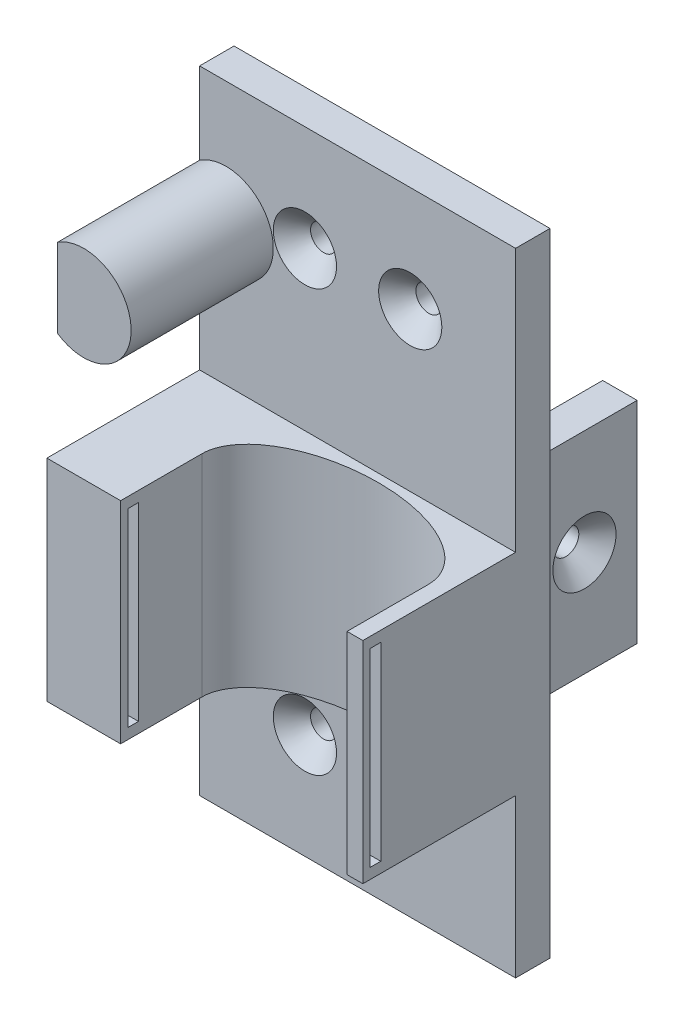
SolidWorks part; units mm, degrees
ref_plane "Front Plane" through (0, 0, 0) normal (0, 0, 1) x (1, 0, 0)
ref_plane "Top Plane" through (0, 0, 0) normal (0, 1, 0) x (1, 0, 0)
ref_plane "Right Plane" through (0, 0, 0) normal (1, 0, 0) x (0, 0, -1)
sketch "Sketch1" plane through (0, 0, 0) normal (0, 0, 1) x (1, 0, 0)
  line L1 (-30, 60) -> (30, 60)
  line L2 (-30, 60) -> (-30, -60)
  line L3 (-30, -60) -> (30, -60)
  line L4 (30, 60) -> (30, -60)
  line L5 (-30, 60) -> (30, -60) construction
  line L6 (-30, -60) -> (30, 60) construction
  point P0 (0, 0)
  dimension "D1" = 60
  dimension "D2" = 120
extrude "Boss-Extrude1" add sketch "Sketch1" along normal blind 6.54
sketch "Sketch7" plane through (0, 0, 6.54) normal (0, 0, 1) x (1, 0, 0)
  line L0 (-30, 60) -> (-30, -60) construction
  line L1 (30, 60) -> (-30, 60) construction
  line L2 (30, -60) -> (30, 60) construction
  line L7 (30, -60) -> (30, 60)
  line L8 (30, 60) -> (-30, 60)
  line L9 (-30, 60) -> (-30, -60)
  line L10 (-30, -60) -> (30, -60)
  line L13 (-30, 44.4833) -> (-30, 29.5167)
  arc A0 (-30, 29.5167) -> (-30, 44.4833) centre (-25, 37) ccw
  dimension "D1" = 9
  dimension "D2" = 23
  dimension "D3" = 55
  dimension "D4" = 0
extrude "Boss-Extrude4" add sketch "Sketch7" along normal blind 27 contours A0 L13
hole_wizard "CSK for M3 Flat Head Machine Screw2" positions "3DSketch1" profile "Sketch9" countersink size "M3" standard "ANSI Metric" end condition through all
sketch3d "3DSketch1"
  line L0 (30, 60, 6.54) -> (-30, 60, 6.54) construction
  line L4 (-30, -60, 6.54) -> (30, -60, 6.54) construction
  line L5 (0, 0, 0) -> (0, 19.3047, 0)
  line L7 (30, -60, 6.54) -> (30, 60, 6.54) construction
  line L8 (-30, 44.4833, 33.54) -> (-30, 29.5167, 33.54) construction
  line L9 (-30, 29.5167, 6.54) -> (-30, -60, 6.54) construction
  point P0 (-10, -40, 6.54)
  point P2 (10, -40, 6.54)
  point P4 (-10, 40, 6.54)
  point P6 (10, 40, 6.54)
  dimension "D1" = 20
  dimension "D2" = 20
  dimension "D3" = 20
  dimension "D6" = 33.6006
  dimension "D4" = 20
  dimension "D5" = 20
  dimension "D9" = 20
  dimension "D7" = 20
  dimension "D8" = 20
sketch "Sketch9" plane through (-10, -40, 6.54) normal (1, 0, 0) x (0, -1, 0)
  line L0 (0, 0) -> (0, 6.54)
  line L1 (0, 6.54) -> (2.465, 6.54)
  line L2 (2.465, 6.54) -> (2.465, 3.535)
  line L3 (2.465, 3.535) -> (6, 0)
  line L5 (6, 0) -> (0, 0)
  line L6 (-2.465, 3.535) -> (-6, 0) construction
  line L11 (0, -6.35) -> (0, 107.95) construction
  dimension "Thru Hole Dia." = 4.93
  dimension "Thru Hole Depth" = 6.54
  dimension "Near C'Sink Dia." = 12
  dimension "Near C'Sink Angle" = 90
sketch "Sketch10" plane through (0, 0, 0) normal (0, 0, -1) x (-1, 0, 0)
  line L1 (20, 20) -> (26.54, 20)
  line L2 (-20, -20) -> (-20, 20)
  line L4 (-20, 20) -> (-26.54, 20)
  line L7 (20, -20) -> (20, 20)
  line L10 (-26.54, 20) -> (-26.54, -20)
  line L11 (-26.54, -20) -> (-20, -20)
  line L12 (26.54, 20) -> (26.54, -20)
  line L13 (26.54, -20) -> (20, -20)
  dimension "D1" = 6.54
  dimension "D2" = 20
  dimension "D3" = 6.54
  dimension "D4" = 20
extrude "Boss-Extrude5" add sketch "Sketch10" along normal blind 20
sketch "Sketch17" plane through (0, 0, 6.54) normal (0, 0, 1) x (1, 0, 0)
  line L0 (-30, 29.5167) -> (-30, -60) construction
  line L1 (-30, 10) -> (30, 10)
  line L2 (-30, 10) -> (-30, -30)
  line L3 (-30, -30) -> (30, -30)
  line L4 (30, 10) -> (30, -30)
  line L5 (30, -60) -> (30, 60) construction
  line L6 (-30, -60) -> (30, -60) construction
  line L7 (30, 60) -> (-30, 60) construction
  dimension "D1" = 40
  dimension "D2" = 30
  dimension "D3" = 50
extrude "Boss-Extrude6" add sketch "Sketch17" along normal blind 29
sketch "Sketch18" plane through (0, 10, 0) normal (0, 1, 0) x (1, 0, 0)
  line L1 (30, -35.54) -> (30, -6.54) construction
  line L2 (30, -35.54) -> (-30, -35.54) construction
  ellipse E0 centre (5.5, -20.092) end of major axis (27, -20.092) minor radius 12
  dimension "D1" = 46
  dimension "D2" = 3
  dimension "D3" = 3.448
extrude "Cut-Extrude1" cut sketch "Sketch18" against normal up to next contours E0
sketch "Sketch21" plane through (0, 0, 35.54) normal (0, 0, 1) x (1, 0, 0)
  line L0 (30, 10) -> (-30, 10) construction
  line L1 (-16, 10) -> (27, 10)
  line L2 (-16, 10) -> (-16, -30)
  line L3 (-16, -30) -> (27, -30)
  line L4 (27, 10) -> (27, -30)
  line L5 (-30, -30) -> (30, -30) construction
  line L6 (30, -30) -> (30, 10) construction
  dimension "D1" = 3
  dimension "D2" = 46
extrude "Cut-Extrude2" cut sketch "Sketch21" against normal up to next contours L2 L3 L4 L1
sketch "Sketch23" plane through (-16, 0, 0) normal (1, 0, 0) x (0, 0, -1)
  line L0 (-35.54, 10) -> (-35.54, -30) construction
  line L1 (-34.14, 8) -> (-32.14, 8)
  line L2 (-34.14, 8) -> (-34.14, -28)
  line L3 (-34.14, -28) -> (-32.14, -28)
  line L4 (-32.14, 8) -> (-32.14, -28)
  line L5 (-20.092, -30) -> (-35.54, -30) construction
  line L6 (-20.092, 10) -> (-35.54, 10) construction
  dimension "D1" = 3.4
  dimension "D2" = 2
  dimension "D3" = 2
  dimension "D4" = 2
  dimension "D5" = 36
extrude "Cut-Extrude3" cut sketch "Sketch23" against normal blind 9
sketch "Sketch24" plane through (27, 0, 0) normal (-1, 0, 0) x (0, 0, 1)
  line L0 (20.092, -30) -> (35.54, -30) construction
  line L1 (32.14, 8) -> (34.14, 8)
  line L2 (32.14, 8) -> (32.14, -28)
  line L3 (32.14, -28) -> (34.14, -28)
  line L4 (34.14, 8) -> (34.14, -28)
  line L5 (20.092, 10) -> (35.54, 10) construction
  line L6 (35.54, 10) -> (35.54, -30) construction
  dimension "D1" = 2
  dimension "D2" = 2
  dimension "D3" = 2
  dimension "D4" = 3.4
extrude "Cut-Extrude4" cut sketch "Sketch24" against normal blind 9
hole_wizard "CSK for M3 Flat Head Machine Screw4" positions "3DSketch2" profile "Sketch27" countersink size "M3" standard "ANSI Metric"
sketch3d "3DSketch2"
  line L0 (-26.54, 20, -20) -> (-26.54, 20, 0) construction
  line L3 (-26.54, -20, -20) -> (-26.54, 20, -20) construction
  point P0 (-26.54, 0, -10)
  point P3 (0, 0, 0)
  point P13 (0, 0, 0)
  dimension "D1" = 20
  dimension "D2" = 10
sketch "Sketch27" plane through (-26.54, 0, -10) normal (0, 1, 0) x (0, 0, 1)
  line L0 (0, 0) -> (0, 6.54)
  line L1 (0, 6.54) -> (2.465, 6.54)
  line L2 (2.465, 6.54) -> (2.465, 3.535)
  line L3 (2.465, 3.535) -> (6, 0)
  line L5 (6, 0) -> (0, 0)
  line L6 (-2.465, 3.535) -> (-6, 0) construction
  line L11 (0, -6.35) -> (0, 107.95) construction
  dimension "Thru Hole Dia." = 4.93
  dimension "Thru Hole Depth" = 6.54
  dimension "Near C'Sink Dia." = 12
  dimension "Near C'Sink Angle" = 90
hole_wizard "CSK for M3 Flat Head Machine Screw5" positions "3DSketch3" profile "Sketch29" countersink size "M3" standard "ANSI Metric" end condition up to next
sketch3d "3DSketch3"
  line L0 (26.54, 20, -20) -> (26.54, 20, 0) construction
  line L1 (26.54, 20, -20) -> (26.54, -20, -20) construction
  point P0 (26.54, 0, -10)
  dimension "D1" = 20
  dimension "D2" = 10
sketch "Sketch29" plane through (26.54, 0, -10) normal (0, 1, 0) x (0, 0, -1)
  line L0 (0, 0) -> (0, 6.54)
  line L1 (0, 6.54) -> (2.465, 6.54)
  line L2 (2.465, 6.54) -> (2.465, 3.535)
  line L3 (2.465, 3.535) -> (6, 0)
  line L5 (6, 0) -> (0, 0)
  line L6 (-2.465, 3.535) -> (-6, 0) construction
  line L11 (0, -6.35) -> (0, 107.95) construction
  dimension "Thru Hole Dia." = 4.93
  dimension "Thru Hole Depth" = 6.54
  dimension "Near C'Sink Dia." = 12
  dimension "Near C'Sink Angle" = 90
